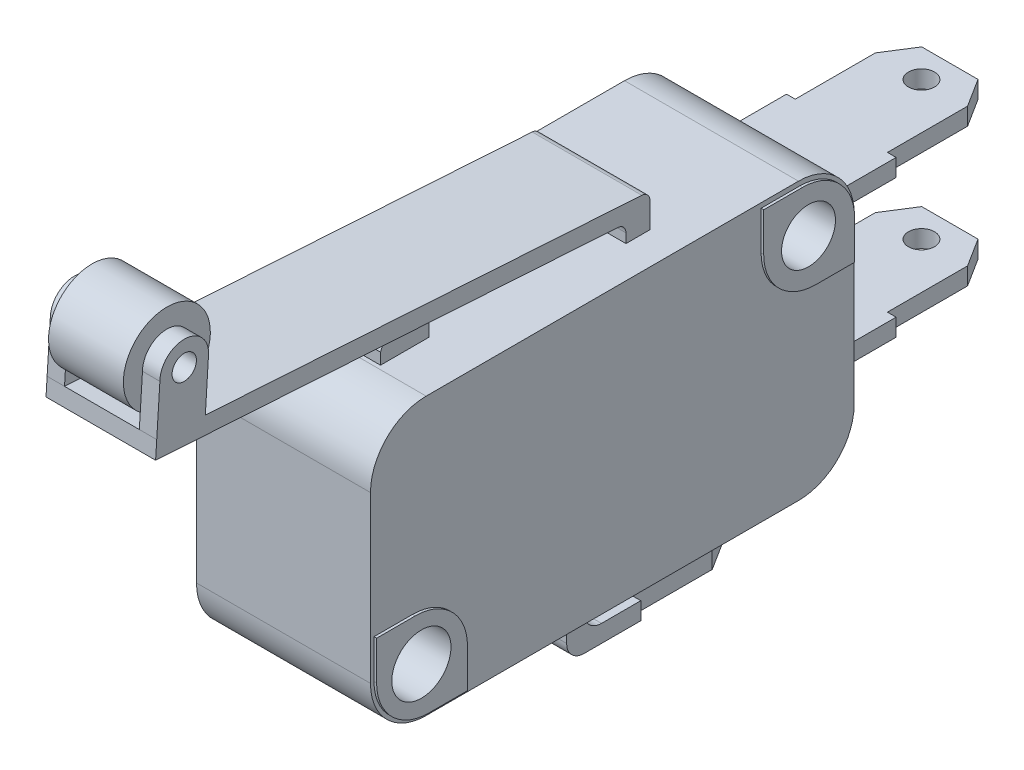
SolidWorks part; units mm, degrees
ref_plane "Plano frontal" through (0, 0, 0) normal (0, 0, 1) x (1, 0, 0)
ref_plane "Plano superior" through (0, 0, 0) normal (0, 1, 0) x (1, 0, 0)
ref_plane "Plano direito" through (0, 0, 0) normal (1, 0, 0) x (0, 0, -1)
sketch "skBlocoBase" plane through (0, 0, 0) normal (1, 0, 0) x (0, 0, -1)
  line L1 (-10.7, 7.95) -> (10.7, 7.95)
  line L2 (-13.9, 4.75) -> (-13.9, -4.75)
  line L3 (-10.7, -7.95) -> (10.7, -7.95)
  line L4 (13.9, 4.75) -> (13.9, -4.75)
  line L5 (-13.9, 7.95) -> (13.9, -7.95) construction
  line L6 (-13.9, -7.95) -> (13.9, 7.95) construction
  arc A0 (-13.9, -4.75) -> (-10.7, -7.95) centre (-10.7, -4.75) ccw
  arc A1 (10.7, -7.95) -> (13.9, -4.75) centre (10.7, -4.75) ccw
  arc A2 (10.7, 7.95) -> (13.9, 4.75) centre (10.7, 4.75) cw
  arc A3 (-10.7, 7.95) -> (-13.9, 4.75) centre (-10.7, 4.75) ccw
  point P0 (0, 0)
  dimension "D3" = 3.2
  dimension "D1" = 27.8
  dimension "D2" = 15.9
extrude "BlocoBase" add sketch "skBlocoBase" along normal mid plane 10
sketch "skFixacao" plane through (0, 0, 0) normal (1, 0, 0) x (0, 0, -1)
  line L0 (-13.9, 0) -> (13.9, 0) construction
  line L1 (-13.9, 4.75) -> (-13.9, -4.75) construction
  line L2 (13.9, -4.75) -> (13.9, 4.75) construction
  circle A0 centre (-11.125, -5.1) radius 1.7
  circle A5 centre (11.125, 5.1) radius 1.55
  dimension "D1" = 3.4
  dimension "D2" = 3.1
  dimension "D3" = 5.1
  dimension "D4" = 5.1
  dimension "D5" = 11.125
  dimension "D6" = 11.125
extrude "Fixacao" cut sketch "skFixacao" against normal mid plane 10.3
sketch "skRessaltoFixacao" plane through (5, 0, 0) normal (1, 0, 0) x (0, 0, -1)
  line L0 (-11.125, -5.1) -> (-9.9229, -6.3021) construction
  line L2 (-11.125, -5.1) -> (-11.125, -6.8) construction
  line L3 (-11.475, -2.325) -> (-13.9, -2.325) construction
  line L6 (-13.9, -2.325) -> (-13.9, -4.75) construction
  line L7 (-8.275, -5.525) -> (-8.275, -7.95) construction
  line L8 (-10.7, -7.95) -> (10.7, -7.95) construction
  line L9 (-8.275, -7.95) -> (-10.7, -7.95) construction
  line L10 (-11.475, -2.525) -> (-13.7, -2.525)
  line L11 (-13.7, -2.525) -> (-13.7, -4.75)
  line L12 (-8.475, -7.75) -> (-10.7, -7.75)
  line L13 (-8.475, -5.525) -> (-8.475, -7.75)
  line L14 (-11.325, -4.6172) -> (-11.325, -6.8)
  line L15 (-11.325, -4.6172) -> (-9.7815, -6.1607)
  line L16 (10.775, -2.525) -> (8.55, -2.525) [skipped]
  line L17 (8.55, -2.525) -> (8.55, -4.75) [skipped]
  line L18 (13.775, -7.75) -> (11.55, -7.75) [skipped]
  line L19 (13.775, -5.525) -> (13.775, -7.75) [skipped]
  line L20 (10.925, -4.6172) -> (10.925, -6.8) [skipped]
  line L21 (10.925, -4.6172) -> (12.4685, -6.1607) [skipped]
  line L22 (11.125, -5.1) -> (12.3271, -6.3021) construction
  line L23 (11.125, -5.1) -> (11.125, -6.8) construction
  line L24 (10.775, -2.325) -> (8.35, -2.325) construction
  line L25 (8.35, -2.325) -> (8.35, -4.75) construction
  line L26 (13.975, -5.525) -> (13.975, -7.95) construction
  line L27 (13.975, -7.95) -> (11.55, -7.95) construction
  line L28 (10.775, 7.675) -> (8.55, 7.675)
  line L29 (8.55, 7.675) -> (8.55, 5.45)
  line L30 (13.775, 2.45) -> (11.55, 2.45)
  line L31 (13.775, 4.675) -> (13.775, 2.45)
  line L32 (10.925, 5.5828) -> (10.925, 3.4)
  line L33 (10.925, 5.5828) -> (12.4685, 4.0393)
  line L34 (11.125, 5.1) -> (12.3271, 3.8979) construction
  line L35 (11.125, 5.1) -> (11.125, 3.4) construction
  line L36 (10.775, 7.875) -> (8.35, 7.875) construction
  line L37 (8.35, 7.875) -> (8.35, 5.45) construction
  line L38 (13.975, 4.675) -> (13.975, 2.25) construction
  line L39 (13.975, 2.25) -> (11.55, 2.25) construction
  line L40 (-11.475, 7.675) -> (-13.7, 7.675) [skipped]
  line L41 (-13.7, 7.675) -> (-13.7, 5.45) [skipped]
  line L42 (-8.475, 2.45) -> (-10.7, 2.45) [skipped]
  line L43 (-8.475, 4.675) -> (-8.475, 2.45) [skipped]
  line L44 (-11.325, 5.5828) -> (-11.325, 3.4) [skipped]
  line L45 (-11.325, 5.5828) -> (-9.7815, 4.0393) [skipped]
  line L46 (-11.125, 5.1) -> (-9.9229, 3.8979) construction
  line L47 (-11.125, 5.1) -> (-11.125, 3.4) construction
  line L48 (-11.475, 7.875) -> (-13.9, 7.875) construction
  line L49 (-13.9, 7.875) -> (-13.9, 5.45) construction
  line L50 (-8.275, 4.675) -> (-8.275, 2.25) construction
  line L51 (-8.275, 2.25) -> (-10.7, 2.25) construction
  arc A0 (-13.9, -4.75) -> (-10.7, -7.95) centre (-10.7, -4.75) ccw construction
  arc A1 (-13.9, -4.75) -> (-10.7, -7.95) centre (-10.7, -4.75) ccw construction
  arc A2 (-11.475, -2.325) -> (-8.275, -5.525) centre (-11.475, -5.525) cw construction
  circle A3 centre (-11.125, -5.1) radius 1.7 construction
  circle A4 centre (-11.125, -5.1) radius 1.7
  arc A7 (-13.7, -4.75) -> (-10.7, -7.75) centre (-10.7, -4.75) ccw
  arc A8 (-11.475, -2.525) -> (-8.475, -5.525) centre (-11.475, -5.525) cw
  circle A9 centre (11.125, -5.1) radius 1.7 [skipped]
  arc A10 (8.55, -4.75) -> (11.55, -7.75) centre (11.55, -4.75) ccw [skipped]
  arc A11 (10.775, -2.525) -> (13.775, -5.525) centre (10.775, -5.525) cw [skipped]
  arc A12 (8.35, -4.75) -> (11.55, -7.95) centre (11.55, -4.75) ccw construction
  arc A13 (10.775, -2.325) -> (13.975, -5.525) centre (10.775, -5.525) cw construction
  circle A14 centre (11.125, 5.1) radius 1.7 construction
  arc A15 (8.55, 5.45) -> (11.55, 2.45) centre (11.55, 5.45) ccw
  arc A16 (10.775, 7.675) -> (13.775, 4.675) centre (10.775, 4.675) cw
  arc A17 (8.35, 5.45) -> (11.55, 2.25) centre (11.55, 5.45) ccw construction
  arc A18 (10.775, 7.875) -> (13.975, 4.675) centre (10.775, 4.675) cw construction
  circle A19 centre (-11.125, 5.1) radius 1.7 [skipped]
  arc A20 (-13.7, 5.45) -> (-10.7, 2.45) centre (-10.7, 5.45) ccw [skipped]
  arc A21 (-11.475, 7.675) -> (-8.475, 4.675) centre (-11.475, 4.675) cw [skipped]
  arc A22 (-13.9, 5.45) -> (-10.7, 2.25) centre (-10.7, 5.45) ccw construction
  arc A23 (-11.475, 7.875) -> (-8.275, 4.675) centre (-11.475, 4.675) cw construction
  circle A24 centre (11.125, 5.1) radius 1.55 construction
  circle A25 centre (11.125, 5.1) radius 1.55
  dimension "D1" = 45
  dimension "D2" = 0.2
  dimension "D3" = 2
  dimension "D4" = 2
extrude "RessaltoFixacao" add sketch "skRessaltoFixacao" along normal blind 0.15
mirror "MirrorRessaltoFixacao" about plane through (0, 0, 0) normal (1, 0, 0) of "RessaltoFixacao"
sketch "skBotao" plane through (0, 0, 0) normal (1, 0, 0) x (0, 0, -1)
  line L0 (-9.075, 9.6) -> (-9.075, -7.95) construction
  line L1 (-10.7, -7.95) -> (10.7, -7.95) construction
  line L2 (-10.475, 7.95) -> (-10.475, 8.6)
  line L3 (10.7, 7.95) -> (-10.7, 7.95) construction
  line L4 (-7.675, 7.95) -> (-7.675, 8.6)
  line L5 (-10.475, 7.95) -> (-7.675, 7.95)
  circle A0 centre (-11.125, -5.1) radius 1.7 construction
  circle A1 centre (11.125, 5.1) radius 1.55 construction
  circle A2 centre (-11.125, -5.1) radius 1.7 construction
  circle A3 centre (11.125, 5.1) radius 1.55 construction
  arc A4 (-10.475, 8.6) -> (-7.675, 8.6) centre (-9.075, 8.12) cw
  point P6 (-9.075, 9.6)
  dimension "D3" = 1.4
  dimension "D1" = 20.2
  dimension "D2" = 14.7
  dimension "D4" = 1
extrude "Botao" add sketch "skBotao" along normal mid plane 4.3
sketch "Sketch5" plane through (0, 0, -13.9) normal (0, 0, -1) x (-1, 0, 0)
  line L0 (-5, 7.95) -> (5, 7.95) construction
  line L1 (-5, 7.95) -> (5, 7.95) construction
  line L2 (-5, 0) -> (5, 0) construction
  line L3 (-5, -4.75) -> (-5, 4.75) construction
  line L4 (5, -4.75) -> (5, 4.75) construction
  line L5 (-5, -7.95) -> (5, -7.95) construction
  line L6 (-5, 3.975) -> (5, 3.975) construction
  line L9 (-5, -3.975) -> (5, -3.975) construction
  line L10 (3.15, -4.475) -> (3.15, -3.475)
  line L11 (-3.15, 4.475) -> (3.15, 4.475)
  line L12 (-3.15, 4.475) -> (-3.15, 3.475)
  line L13 (-3.15, 3.475) -> (3.15, 3.475)
  line L14 (3.15, 4.475) -> (3.15, 3.475)
  line L15 (-3.15, 4.475) -> (3.15, 3.475) construction
  line L16 (-3.15, 3.475) -> (3.15, 4.475) construction
  line L17 (-3.15, -3.475) -> (3.15, -3.475)
  line L18 (-3.15, -4.475) -> (-3.15, -3.475)
  line L19 (-3.15, -4.475) -> (3.15, -4.475)
  point P14 (0, 3.975)
  dimension "D1" = 3.975
  dimension "D2" = 1
  dimension "D3" = 6.3
extrude "BaseConectorNONC" add sketch "Sketch5" along normal blind 10.5
sketch "skDesenhoConectorNONC" plane through (0, -4.475, 0) normal (0, -1, 0) x (1, 0, 0)
  line L0 (0, -24.4) -> (0, -13.9) construction
  line L1 (3.15, -24.4) -> (-3.15, -24.4) construction
  line L2 (3.15, -13.9) -> (-3.15, -13.9) construction
  line L3 (1.617, -24.4) -> (-1.617, -24.4)
  line L4 (3.15, -13.9) -> (-3.15, -13.9)
  line L5 (-3.15, -13.9) -> (-3.15, -18.1612)
  line L6 (-3.15, -24.4) -> (-3.15, -13.9) construction
  line L7 (-3.15, -18.1612) -> (-2.65, -18.1612)
  line L8 (-2.65, -18.1612) -> (-2.65, -22.7671)
  line L9 (-2.65, -22.7671) -> (-1.617, -24.4)
  line L10 (2.65, -22.7671) -> (1.617, -24.4)
  line L11 (2.65, -18.1612) -> (2.65, -22.7671)
  line L12 (3.15, -18.1612) -> (2.65, -18.1612)
  line L13 (3.15, -13.9) -> (3.15, -18.1612)
  line L14 (-3.15, -18.1612) -> (-3.15, -24.4)
  line L15 (-3.15, -24.4) -> (-1.617, -24.4)
  line L16 (1.617, -24.4) -> (3.15, -24.4)
  line L17 (3.15, -24.4) -> (3.15, -18.1612)
  circle A0 centre (0, -22.7671) radius 0.75
  line M2 (-3.15, -13.9) -> (-3.15, -24.4)
  line M3 (-3.15, -24.4) -> (3.15, -24.4)
  line M4 (3.15, -24.4) -> (3.15, -13.9)
  dimension "D1" = 0.5
extrude "DesenhoConectorNONC" cut sketch "skDesenhoConectorNONC" against normal blind 20.5 contours L12 L11 L10 M4 M3 | L9 L8 L7 M2 M3 | A0 L0 | L0 A0
sketch "skBaseConectorCOM" plane through (0, 0, 0) normal (1, 0, 0) x (0, 0, -1)
  line L0 (10.7, 7.95) -> (-10.7, 7.95) construction
  line L1 (9.725, -11.25) -> (0.225, -11.25)
  line L2 (-0.775, -10.25) -> (-0.775, -7.95)
  line L3 (-10.7, -7.95) -> (10.7, -7.95) construction
  line L4 (9.725, -10.25) -> (1.225, -10.25)
  line L5 (0.225, -9.25) -> (0.225, -7.95)
  line L6 (9.725, -10.25) -> (9.725, -11.25)
  line L7 (0.225, -7.95) -> (-0.775, -7.95)
  circle A0 centre (-11.125, -5.1) radius 1.7 construction
  circle A1 centre (11.125, 5.1) radius 1.55 construction
  circle A2 centre (-11.125, -5.1) radius 1.7 construction
  circle A3 centre (11.125, 5.1) radius 1.55 construction
  arc A4 (1.225, -10.25) -> (0.225, -9.25) centre (1.225, -9.25) cw
  arc A5 (0.225, -11.25) -> (-0.775, -10.25) centre (0.225, -10.25) cw
  point P6 (9.725, -11.25)
  point P22 (-0.775, -11.25)
  dimension "D5" = 1
  dimension "D1" = 19.2
  dimension "D2" = 1.4
  dimension "D3" = 10.5
  dimension "D4" = 1
extrude "BaseConectorCOM" add sketch "skBaseConectorCOM" along normal mid plane 6.3
sketch "skDesenhoConectorCOM" plane through (0, -11.25, 0) normal (0, -1, 0) x (1, 0, 0)
  line L0 (0, -9.725) -> (0, 0.775) construction
  line L1 (1.617, -9.725) -> (-1.617, -9.725)
  line L2 (3.15, 0.775) -> (-3.15, 0.775)
  line L3 (-3.15, 0.775) -> (-3.15, -3.4862)
  line L4 (-3.15, -3.4862) -> (-2.65, -3.4862)
  line L5 (-2.65, -3.4862) -> (-2.65, -8.0921)
  line L6 (-2.65, -8.0921) -> (-1.617, -9.725)
  line L7 (2.65, -8.0921) -> (1.617, -9.725)
  line L8 (2.65, -3.4862) -> (2.65, -8.0921)
  line L9 (3.15, -3.4862) -> (2.65, -3.4862)
  line L10 (3.15, 0.775) -> (3.15, -3.4862)
  line L11 (-3.15, -3.4862) -> (-3.15, -9.725)
  line L12 (-3.15, -9.725) -> (-1.617, -9.725)
  line L13 (1.617, -9.725) -> (3.15, -9.725)
  line L14 (3.15, -9.725) -> (3.15, -3.4862)
  circle A0 centre (0, -8.0921) radius 0.75
  line M1 (-3.15, -0.225) -> (-3.15, -9.725)
  line M2 (-3.15, -9.725) -> (3.15, -9.725)
  line M3 (3.15, -9.725) -> (3.15, -0.225)
  dimension "D1" = 0.5
extrude "DesenhoConectorCOM" cut sketch "skDesenhoConectorCOM" against normal up to surface (1 mm away) contours L9 L8 L7 M3 M2 | L0 A0 | A0 L0 | L6 L5 L4 M1 M2
sketch "skBaseContato" plane through (0, 0, 0) normal (1, 0, 0) x (0, 0, -1)
  line L0 (2.633, 7.95) -> (2.633, 8.4866)
  line L1 (10.7, 7.95) -> (-10.7, 7.95) construction
  line L2 (2.1649, 8.9856) -> (-24.4, 10.6816)
  line L3 (-24.4, 10.6816) -> (-24.3363, 11.6796)
  line L4 (-24.3363, 11.6796) -> (3.5456, 9.8995)
  line L5 (4.0137, 9.4005) -> (4.0137, 7.95)
  line L6 (4.0137, 7.95) -> (2.633, 7.95)
  line L7 (-13.9, 4.75) -> (-13.9, -4.75) construction
  arc A0 (-7.675, 8.6) -> (-10.475, 8.6) centre (-9.075, 8.12) ccw construction
  arc A1 (-7.675, 8.6) -> (-10.475, 8.6) centre (-9.075, 8.12) ccw construction
  arc A2 (3.5456, 9.8995) -> (4.0137, 9.4005) centre (3.5137, 9.4005) cw
  arc A3 (2.633, 8.4866) -> (2.1649, 8.9856) centre (2.133, 8.4866) ccw
  dimension "D4" = 0.5
  dimension "D1" = 1
  dimension "D2" = 0.1
  dimension "D3" = 10.5
extrude "BaseContato" add sketch "skBaseContato" along normal mid plane 6.3
sketch "skApoioRolo" plane through (3.15, 0, 0) normal (1, 0, 0) x (0, 0, -1)
  line L0 (-22.9391, 11.5904) -> (-22.6936, 15.4355) construction
  line L1 (3.5456, 9.8995) -> (-24.3363, 11.6796) construction
  line L2 (-24.3363, 11.6796) -> (-24.4, 10.6816) construction
  line L3 (-24.1542, 14.4868) -> (-24.3363, 11.6796)
  line L4 (-24.3363, 11.6796) -> (-22.9391, 11.5904)
  line L5 (-22.9391, 11.5904) -> (-21.542, 11.5012)
  line L6 (-21.542, 11.5012) -> (-21.3542, 14.4868)
  arc A0 (-21.3652, 14.3114) -> (-24.1542, 14.4868) centre (-22.7542, 14.4868) ccw
  circle A1 centre (-22.7542, 14.4868) radius 0.7
  dimension "D1" = 1.4
extrude "ApoioRolo" add sketch "skApoioRolo" against normal blind 1
mirror "MirrorApoioRolo" about plane through (0, 0, 0) normal (1, 0, 0) of "ApoioRolo"
sketch "skRolo" plane through (2.15, 0, 0) normal (-1, 0, 0) x (0, 0, 1)
  circle A0 centre (22.7542, 14.4868) radius 2.5
extrude "Rolo" add sketch "skRolo" along normal offset from surface (4.3 mm away) 1 up to face at (-3.15, 10.6449, 8.7805)
